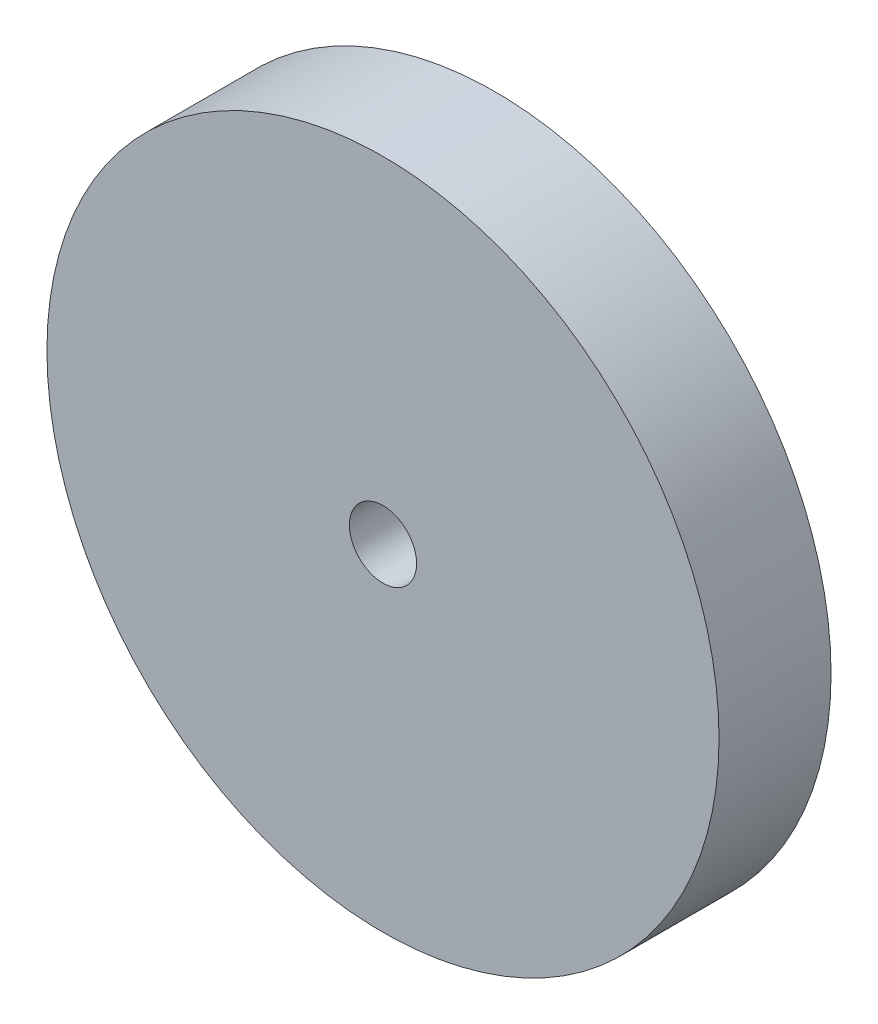
SolidWorks part; units mm, degrees
ref_plane "Front Plane" through (0, 0, 0) normal (0, 0, 1) x (1, 0, 0)
ref_plane "Top Plane" through (0, 0, 0) normal (0, 1, 0) x (1, 0, 0)
ref_plane "Right Plane" through (0, 0, 0) normal (1, 0, 0) x (0, 0, -1)
sketch "Sketch1" plane through (0, 0, 0) normal (0, 0, 1) x (1, 0, 0)
  circle A0 centre (0, 0) radius 60
  dimension "D1" = 120
extrude "Boss-Extrude1" add sketch "Sketch1" along normal blind 20
sketch "Sketch2" plane through (0, 0, 20) normal (0, 0, 1) x (1, 0, 0)
  circle A0 centre (0, 0) radius 6
  dimension "D1" = 12
extrude "Cut-Extrude1" cut sketch "Sketch2" against normal through all
